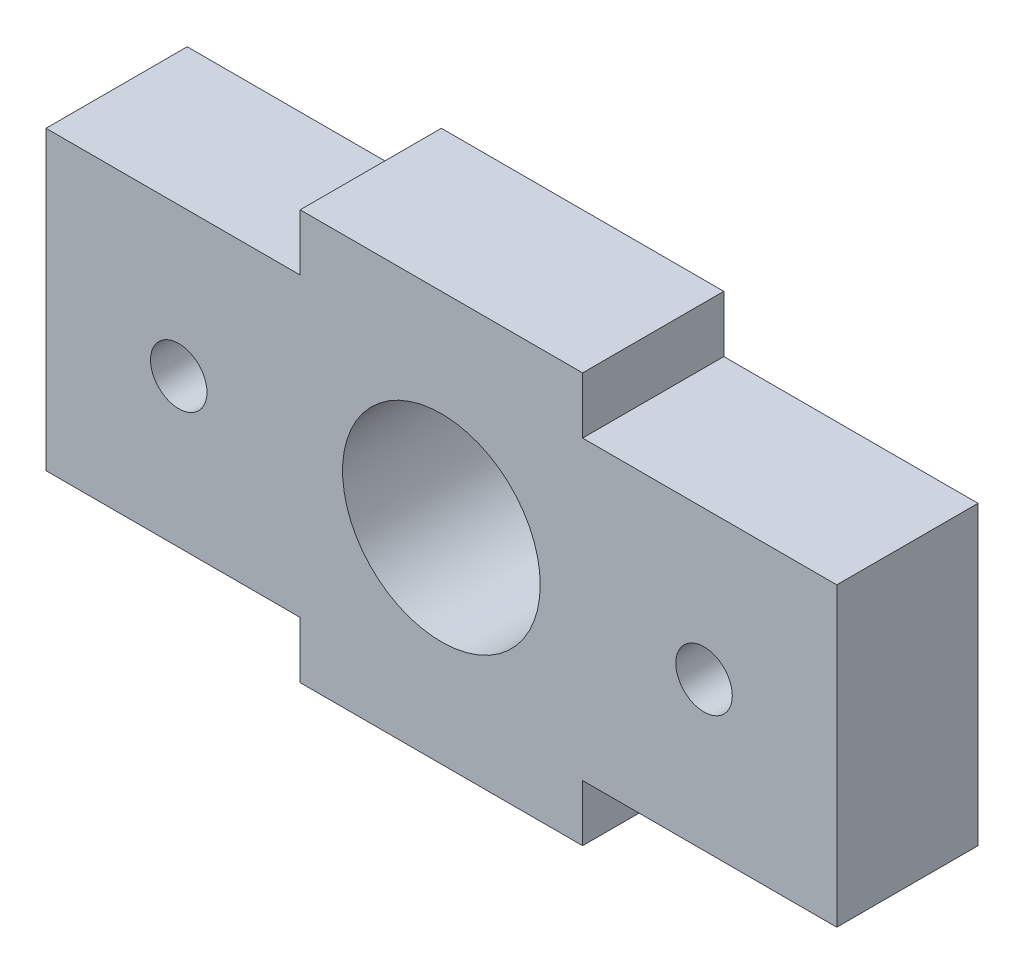
SolidWorks part; units mm, degrees
ref_plane "Front Plane" through (0, 0, 0) normal (0, 0, 1) x (1, 0, 0)
ref_plane "Top Plane" through (0, 0, 0) normal (0, 1, 0) x (1, 0, 0)
ref_plane "Right Plane" through (0, 0, 0) normal (1, 0, 0) x (0, 0, -1)
sketch "Sketch1" plane through (0, 0, 0) normal (0, 0, 1) x (1, 0, 0)
  line L0 (-14, -5.25) -> (14, 5.25) construction
  line L1 (-14, -5.25) -> (14, -5.25)
  line L2 (-14, -5.25) -> (-14, 5.25)
  line L3 (-14, 5.25) -> (14, 5.25)
  line L4 (14, -5.25) -> (14, 5.25)
  line L5 (14, -5.25) -> (0, 0) construction
  line L6 (0, 0) -> (-14, 5.25) construction
  line L7 (0, 0) -> (9.3, 0) construction
  line L8 (0, 5.25) -> (0, 0) construction
  line L9 (0, 0) -> (0, -5.25) construction
  line L10 (-5, 5.25) -> (-5, 7.25)
  line L11 (-5, 7.25) -> (5, 7.25)
  line L12 (5, 7.25) -> (5, 5.25)
  line L13 (0, 7.25) -> (0, 5.25) construction
  line L14 (-5, -5.25) -> (-5, -7.25)
  line L15 (5, -7.25) -> (5, -5.25)
  line L16 (-5, -7.25) -> (5, -7.25)
  circle A0 centre (0, 0) radius 3.5
  circle A1 centre (9.3, 0) radius 1
  circle A2 centre (-9.3, 0) radius 1
  dimension "D3" = 7
  dimension "D5" = 2
  dimension "D1" = 10.5
  dimension "D2" = 28
  dimension "D4" = 9.3
  dimension "D6" = 2
  dimension "D7" = 10
extrude "Boss-Extrude1" add sketch "Sketch1" along normal blind 5 contours L1 L4 L3 L2 A0 A1 A2 | L12 L11 L10 L3 | L14 L16 L15 L1
